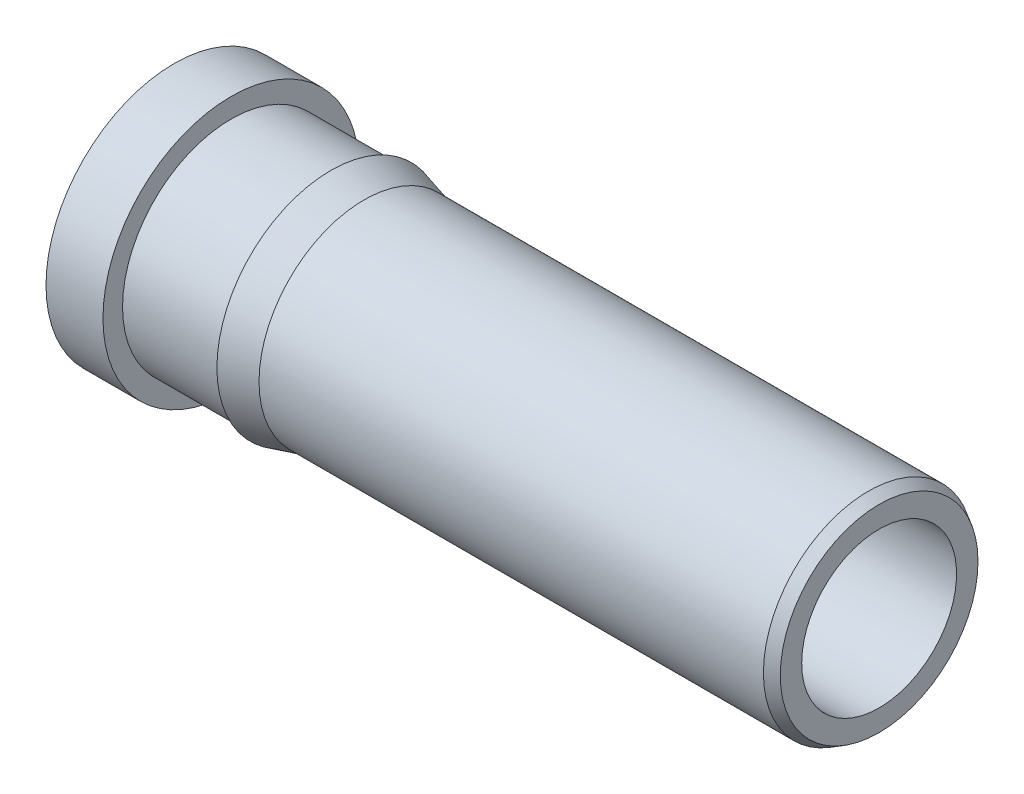
SolidWorks part; units mm, degrees
material "Brass Alloy 385"
ref_plane "Front Plane" through (0, 0, 0) normal (0, 0, 1) x (1, 0, 0)
ref_plane "Top Plane" through (0, 0, 0) normal (0, 1, 0) x (1, 0, 0)
ref_plane "Right Plane" through (0, 0, 0) normal (1, 0, 0) x (0, 0, -1)
sketch "Sketch1" plane through (0, 0, 0) normal (0, 0, 1) x (1, 0, 0)
  line L0 (0, 0) -> (0, 0.9144)
  line L1 (0, 0.9144) -> (0.4064, 0.9144)
  line L2 (0.4064, 0.9144) -> (0.4064, 0.7747)
  line L3 (0.4064, 0.7747) -> (1.1176, 0.7747)
  line L4 (1.1176, 0.7747) -> (1.1176, 0.8128)
  line L5 (1.1176, 0.8128) -> (1.3546, 0.7493)
  line L6 (1.3546, 0.7493) -> (4.953, 0.7493)
  line L7 (4.953, 0.7493) -> (5.0292, 0.7053)
  line L8 (5.0292, 0.7053) -> (5.0292, 0)
  line L9 (0, 0) -> (5.0292, 0)
  line L10 (0, 0) -> (5.0292, 0) construction
revolve "RevolutionAngle1" add sketch "Sketch1" angle 360 about L10
hole_wizard "Hole1" positions "Sketch3" profile "Sketch2" legacy
sketch "Sketch3" plane through (0, 0, 0) normal (-1, 0, 0) x (0, 0, 1)
  point P0 (0, 0)
sketch "Sketch2" plane through (0, 0, 0) normal (0, 1, 0) x (0, 0, 1)
  line L0 (0, 0) -> (0, 3.5388)
  line L1 (0, 3.5388) -> (0.6477, 3.1496)
  line L2 (0.6477, 3.1496) -> (0.6477, 0)
  line L4 (0.6477, 0) -> (0, 0)
  line L6 (0, 3.5388) -> (-0.6477, 3.1496) construction
  line L7 (0, -4.2442) -> (0, 117.3081) construction
  dimension "Diameter" = 1.2954
  dimension "Depth" = 3.1496
  dimension "Drill Angle" = 118
hole_wizard "Hole2" positions "Sketch5" profile "Sketch4" legacy end condition through all
sketch "Sketch5" plane through (0, 0.3406, -0.6478) normal (-1, 0, 0) x (0, 0, 1)
  point P0 (0.6478, -0.3406)
sketch "Sketch4" plane through (0, 0, 0) normal (0, 1, 0) x (0, 0, 1)
  line L0 (0, 0) -> (0, 5.3611)
  line L1 (0, 5.3611) -> (0.5524, 5.0292)
  line L2 (0.5524, 5.0292) -> (0.5524, 0)
  line L4 (0.5524, 0) -> (0, 0)
  line L6 (0, 5.3611) -> (-0.5524, 5.0292) construction
  line L7 (0, -4.2442) -> (0, 117.3081) construction
  dimension "Diameter" = 1.1049
  dimension "Depth" = 5.0292
  dimension "Drill Angle" = 118
